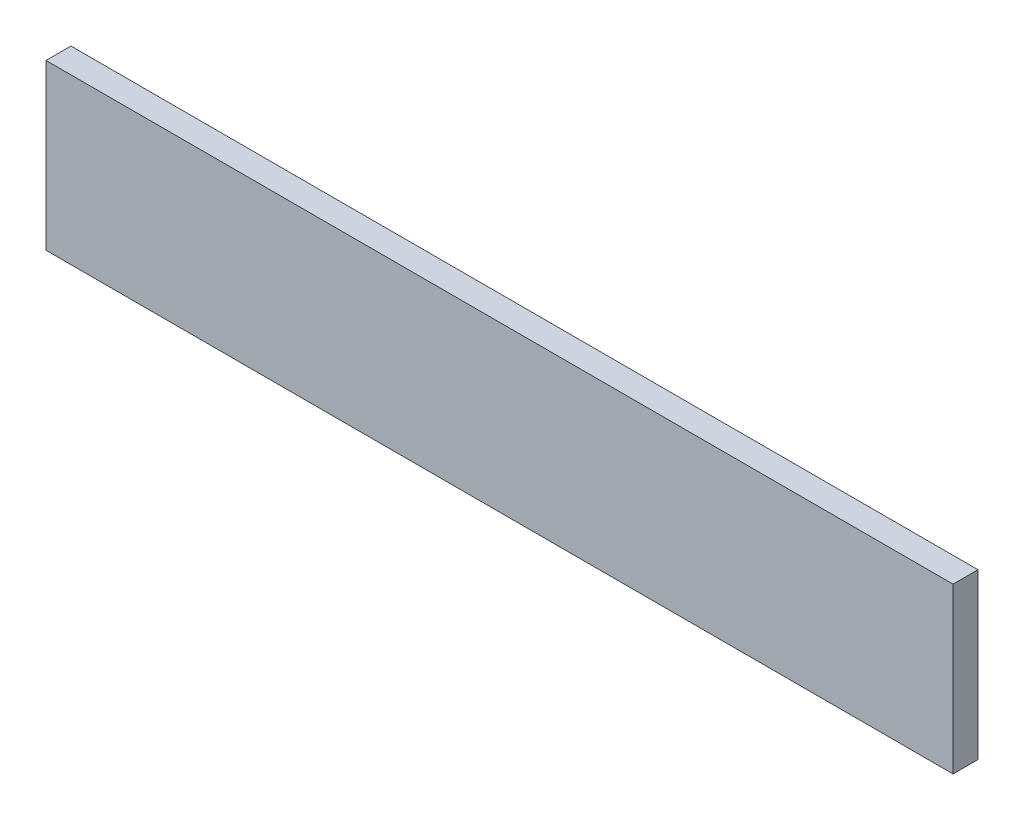
SolidWorks part; units mm, degrees
material "Pine"
ref_plane "Front Plane" through (0, 0, 0) normal (0, 0, 1) x (1, 0, 0)
ref_plane "Top Plane" through (0, 0, 0) normal (0, 1, 0) x (1, 0, 0)
ref_plane "Right Plane" through (0, 0, 0) normal (1, 0, 0) x (0, 0, -1)
sketch "Sketch1" plane through (0, 0, 0) normal (0, 0, 1) x (1, 0, 0)
  line L0 (-400, -20) -> (-400, 0)
  line L1 (380, 0) -> (-380, 0)
  line L2 (400, -20) -> (400, -145)
  line L3 (400, -145) -> (-400, -145)
  line L4 (-400, -20) -> (-400, -145)
  line L5 (-400, 0) -> (-380, 0)
  line L6 (400, -20) -> (400, 0)
  line L7 (400, 0) -> (380, 0)
  point P0 (400, 0)
  point P3 (-400, 0)
  point P5 (0, -145)
  dimension "D1" = 145
  dimension "D2" = 800
extrude "Boss-Extrude1" add sketch "Sketch1" along normal blind 22
